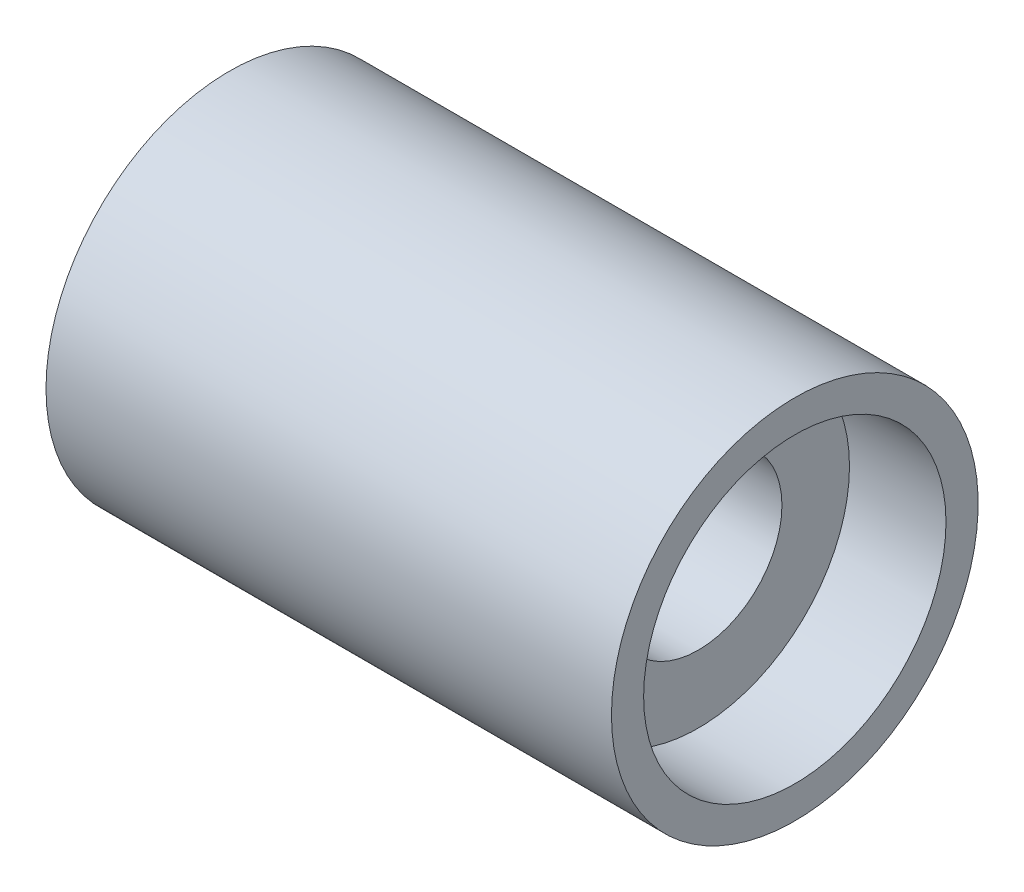
SolidWorks part; units mm, degrees
ref_plane "Plan de face" through (0, 0, 0) normal (0, 0, 1) x (1, 0, 0)
ref_plane "Plan de dessus" through (0, 0, 0) normal (0, 1, 0) x (1, 0, 0)
ref_plane "Plan de droite" through (0, 0, 0) normal (1, 0, 0) x (0, 0, -1)
sketch "Esquisse1" plane through (0, 0, 0) normal (0, 0, 1) x (1, 0, 0)
  line L5 (28.95, 13) -> (28.95, 23.5)
  line L6 (-43.95, 23.5) -> (-28.95, 23.5)
  line L11 (-43.95, 23.5) -> (-43.95, 28.5)
  line L12 (-43.95, 28.5) -> (43.95, 28.5)
  line L14 (43.95, 23.5) -> (43.95, 28.5)
  line L15 (-43.95, 23.5) -> (43.95, 28.5) construction
  line L16 (-43.95, 28.5) -> (43.95, 23.5) construction
  line L17 (28.95, 13) -> (-28.95, 13)
  line L19 (-28.95, 13) -> (-28.95, 23.5)
  line L20 (28.95, 13) -> (-28.95, 23.5) construction
  line L21 (28.95, 23.5) -> (-28.95, 13) construction
  line L22 (28.95, 23.5) -> (43.95, 23.5)
  line L23 (0, 0) -> (0, 52) construction
  line L24 (-28.0106, 0) -> (28.8531, 0) construction
  point P0 (0, 26)
  point P6 (-43.95, 26)
  point P7 (0, 18.25)
  dimension "D1" = 28.5
  dimension "D2" = 23.5
  dimension "D3" = 13
  dimension "D4" = 87.9
  dimension "D5" = 15
revolve "Révolution1" add sketch "Esquisse1" angle 360 about L24
sketch "Esquisse2" plane through (0, 0, 0) normal (1, 0, 0) x (0, 0, -1)
  line L0 (0, 20.8645) -> (0, -27.6523)
ref_plane "Plan1" through (0, 0, 0) normal (0.9781, 0, 0.2079) x (0, -1, 0)
